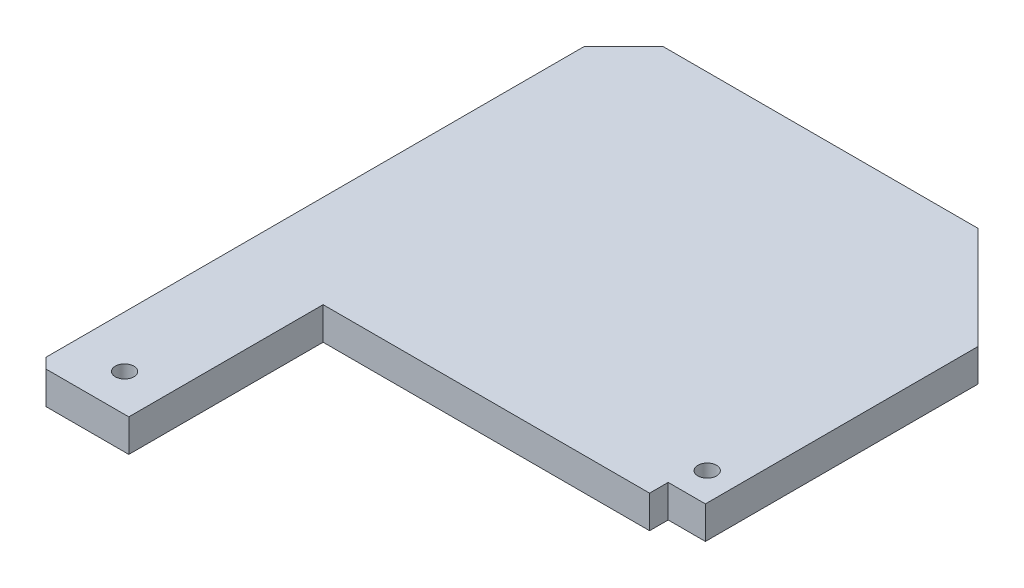
SolidWorks part; units mm, degrees
ref_plane "Front Plane" through (0, 0, 0) normal (0, 0, 1) x (1, 0, 0)
ref_plane "Top Plane" through (0, 0, 0) normal (0, 1, 0) x (1, 0, 0)
ref_plane "Right Plane" through (0, 0, 0) normal (1, 0, 0) x (0, 0, -1)
sketch "Sketch1" plane through (0, 0, 0) normal (0, 1, 0) x (1, 0, 0)
  line L1 (21.15, -21.15) -> (-21.15, -21.15)
  line L2 (21.15, -21.15) -> (21.15, 21.15)
  line L3 (21.15, 21.15) -> (-21.15, 21.15)
  line L4 (-21.15, -21.15) -> (-21.15, 21.15)
  line L5 (21.15, -21.15) -> (-21.15, 21.15) construction
  line L6 (21.15, 21.15) -> (-21.15, -21.15) construction
  point P0 (0, 0)
  dimension "D1" = 42.3
extrude "Boss-Extrude1" add sketch "Sketch1" along normal blind 3.5
sketch "Sketch2" plane through (0, 3.5, 0) normal (0, 1, 0) x (1, 0, 0)
  line L0 (-21.15, 16.9074) -> (-16.9074, 21.15)
  line L1 (-21.15, 21.15) -> (-21.15, -21.15) construction
  line L2 (21.15, 21.15) -> (-21.15, 21.15) construction
  line L3 (-16.9074, 21.15) -> (-21.15, 21.15)
  line L4 (-21.15, 21.15) -> (-21.15, 16.9074)
  dimension "D1" = 6
extrude "Cut-Extrude1" cut sketch "Sketch2" against normal up to next (3.5 mm away)
sketch "Sketch3" plane through (0, 0, 0) normal (0, 0, 1) x (1, 0, 0)
  line L0 (0, 0) -> (0, 11.8048) construction
pattern_circular "CirPattern1" count 4 over 360 about axis through (0, 0, 0) along (0, 1, 0) of "Cut-Extrude1"
sketch "Sketch5" plane through (21.15, 0, 0) normal (1, 0, 0) x (0, 0, -1)
  line L1 (-21.15, 3.5) -> (21.15, 3.5)
  line L2 (-21.15, 3.5) -> (-21.15, 0)
  line L3 (-21.15, 0) -> (21.15, 0)
  line L12 (21.15, 3.5) -> (21.15, 0)
extrude "Boss-Extrude3" add sketch "Sketch5" along normal blind 6.79 and the other way blind 6.79
sketch "Sketch6" plane through (0, 3.5, 0) normal (0, 1, 0) x (1, 0, 0)
  line L0 (23.94, -21.15) -> (23.94, -19.15)
  line L1 (-16.9074, -21.15) -> (27.94, -21.15) construction
  line L2 (23.94, -19.15) -> (27.94, -19.15)
  line L3 (27.94, 21.15) -> (27.94, -21.15) construction
  line L4 (23.94, -21.15) -> (27.94, -21.15)
  line L5 (27.94, -21.15) -> (27.94, -19.15)
  dimension "D1" = 2
  dimension "D2" = 4
extrude "Cut-Extrude2" cut sketch "Sketch6" against normal up to next
sketch "Sketch7" plane through (0, 3.5, 0) normal (0, 1, 0) x (1, 0, 0)
  line L0 (-21.15, -16.9074) -> (-21.15, -42.0365)
  line L1 (-21.15, -42.0365) -> (-11.15, -42.0365)
  line L2 (-11.15, -42.0365) -> (-11.15, -21.15)
  line L3 (-16.9074, -21.15) -> (23.94, -21.15) construction
  line L4 (-11.15, -21.15) -> (-16.9074, -21.15)
  line L5 (-16.9074, -21.15) -> (-21.15, -16.9074)
  line L7 (-20.0571, -42.0365) -> (-16.0571, -42.0365) construction
  dimension "D1" = 10
extrude "Boss-Extrude4" add sketch "Sketch7" against normal up to surface (3.5 mm away) up to face at (3.4557, 0, 4.7875)
chamfer "Chamfer1" distance 1.1 angle 45 1 edges at (-21.15, 1.75, 42.0365)
sketch "Sketch8" plane through (0, 0, 0) normal (0, -1, 0) x (1, 0, 0)
  line L0 (-11.15, 42.0365) -> (-20.05, 42.0365) construction
  circle A0 centre (-15.6, 38.0365) radius 1
  point P4 (-15.6, 42.0365)
  dimension "D2" = 2
  dimension "D1" = 4
extrude "Cut-Extrude3" cut sketch "Sketch8" against normal up to surface (3.5 mm away) up to face at (0.2203, 3.5, 14.6402)
chamfer "Chamfer2" distance 11 angle 45 1 edges at (27.94, 1.75, -21.15)
sketch "Sketch10" plane through (0, 0, 0) normal (0, -1, 0) x (1, 0, 0)
  line L0 (27.94, 19.15) -> (23.94, 19.15) construction
  line L1 (27.94, -10.15) -> (27.94, 19.15) construction
  circle A0 centre (24.94, 15.9565) radius 1
  dimension "D1" = 2
  dimension "D2" = 3.1935
  dimension "D3" = 3
extrude "Cut-Extrude4" cut sketch "Sketch10" against normal up to surface (3.5 mm away) up to face at (-15.6, 3.5, 39.0365)
